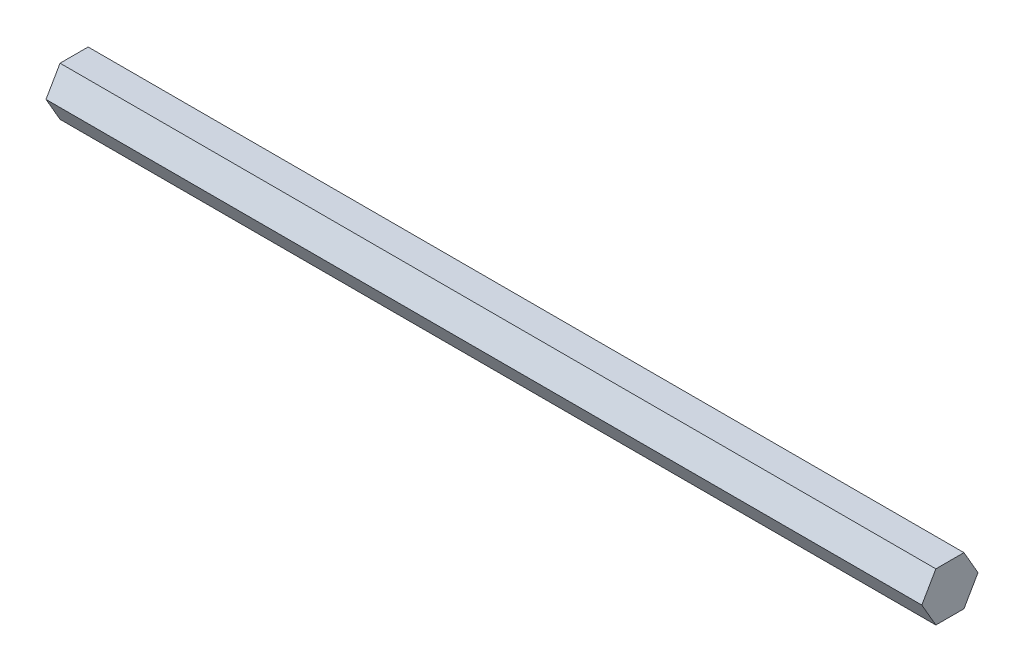
SolidWorks part; units mm, degrees
ref_plane "Front Plane" through (0, 0, 0) normal (0, 0, 1) x (1, 0, 0)
ref_plane "Top Plane" through (0, 0, 0) normal (0, 1, 0) x (1, 0, 0)
ref_plane "Right Plane" through (0, 0, 0) normal (1, 0, 0) x (0, 0, -1)
sketch "Sketch1" plane through (0, 0, 0) normal (1, 0, 0) x (0, 0, -1)
  line L1 (7.3323, 0) -> (3.6662, 6.35)
  line L2 (3.6662, 6.35) -> (-3.6662, 6.35)
  line L3 (-3.6662, 6.35) -> (-7.3323, 0)
  line L4 (-7.3323, 0) -> (-3.6662, -6.35)
  line L5 (-3.6662, -6.35) -> (3.6662, -6.35)
  line L6 (3.6662, -6.35) -> (7.3323, 0)
  circle A0 centre (0, 0) radius 6.35 construction
extrude "Boss-Extrude1" add sketch "Sketch1" along normal blind 228.6
